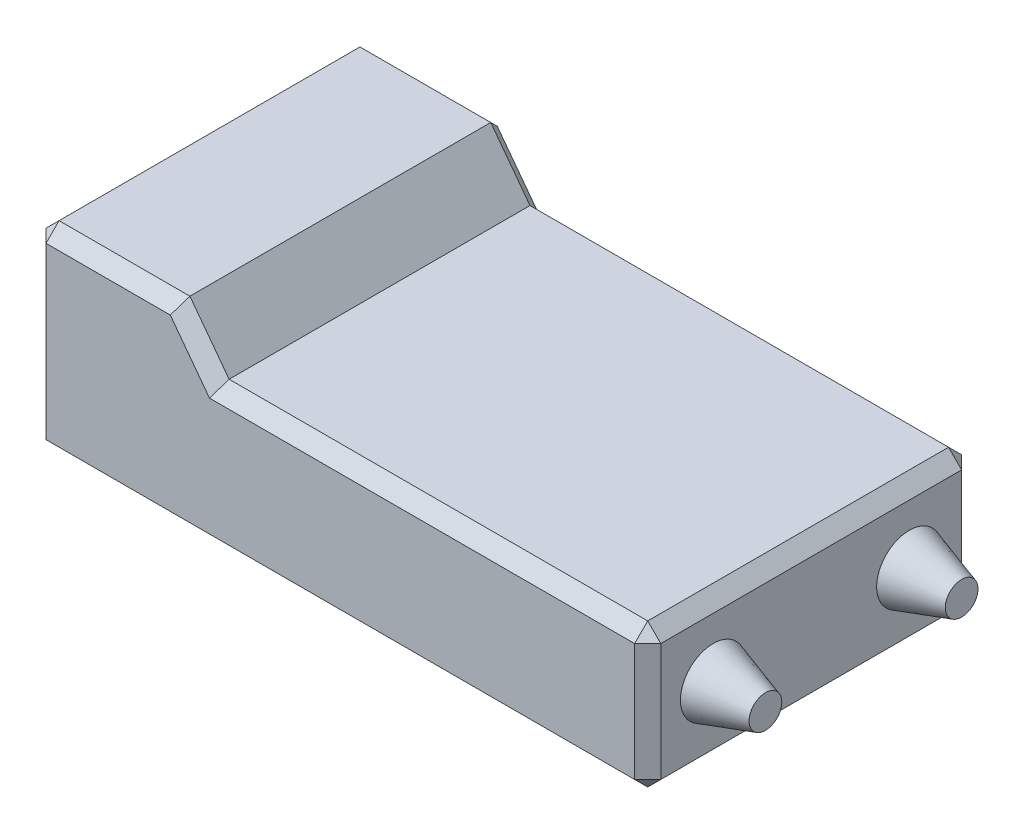
SolidWorks part; units mm, degrees
ref_plane "Front Plane" through (0, 0, 0) normal (0, 0, 1) x (1, 0, 0)
ref_plane "Top Plane" through (0, 0, 0) normal (0, 1, 0) x (1, 0, 0)
ref_plane "Right Plane" through (0, 0, 0) normal (1, 0, 0) x (0, 0, -1)
sketch "Sketch2" plane through (0, 0, 0) normal (0, 1, 0) x (1, 0, 0)
  line L1 (-23.5, 12.5) -> (23.5, 12.5)
  line L2 (-23.5, 12.5) -> (-23.5, -12.5)
  line L3 (-23.5, -12.5) -> (23.5, -12.5)
  line L4 (23.5, 12.5) -> (23.5, -12.5)
  line L5 (-23.5, 12.5) -> (23.5, -12.5) construction
  line L6 (-23.5, -12.5) -> (23.5, 12.5) construction
  point P0 (0, 0)
  dimension "D1" = 25
  dimension "D2" = 47
extrude "Boss-Extrude1" add sketch "Sketch2" along normal blind 11
sketch "Sketch3" plane through (0, 0, 12.5) normal (0, 0, 1) x (1, 0, 0)
  line L0 (-23.5, 11) -> (-9.5, 11)
  line L1 (-23.5, 11) -> (23.5, 11) construction
  line L2 (-9.5, 11) -> (-12.5, 15)
  line L3 (-12.5, 15) -> (-23.5, 15)
  line L4 (-23.5, 15) -> (-23.5, 11)
  dimension "D1" = 11
  dimension "D2" = 14
  dimension "D3" = 4
extrude "Boss-Extrude2" add sketch "Sketch3" against normal up to surface (25 mm away) up to face at (0, 5.5, -12.5)
sketch "Sketch4" plane through (-23.5, 0, 0) normal (-1, 0, 0) x (0, 0, 1)
  line L0 (-12.5, 15) -> (12.5, 15) construction
  line L1 (-10.5, 13) -> (10.5, 13)
  line L2 (-10.5, 13) -> (-10.5, 2)
  line L3 (-10.5, 2) -> (10.5, 2)
  line L4 (10.5, 13) -> (10.5, 2)
  line L5 (-10.5, 13) -> (10.5, 2) construction
  line L6 (-10.5, 2) -> (10.5, 13) construction
  line L7 (12.5, 15) -> (12.5, 0) construction
  line L8 (-12.5, 15) -> (-12.5, 0) construction
  line L9 (-12.5, 0) -> (12.5, 0) construction
  point P0 (0, 7.5)
  dimension "D1" = 2
  dimension "D2" = 2
  dimension "D3" = 2
  dimension "D4" = 2
extrude "Cut-Extrude1" cut sketch "Sketch4" against normal blind 5
sketch "Sketch5" plane through (23.5, 0, 0) normal (1, 0, 0) x (0, 0, -1)
  line L0 (-12.5, 11) -> (-12.5, 0) construction
  line L1 (-12.5, 0) -> (12.5, 0) construction
  circle A0 centre (-7.5, 5.5) radius 2.5
  dimension "D1" = 5
  dimension "D2" = 5
  dimension "D3" = 5.5
ref_plane "Plane1" through (27.5, 0, 0) normal (1, 0, 0) x (0, 0, -1)
sketch "Sketch6" plane through (27.5, 0, 0) normal (1, 0, 0) x (0, 0, -1)
  circle A0 centre (-7.5, 5.5) radius 1.25
  dimension "D1" = 2.5
loft "Loft1" add profiles "Sketch5", "Sketch6"
mirror "Mirror1" about plane through (0, 0, 0) normal (0, 0, 1) of "Loft1"
chamfer "Chamfer1" distance 1 angle 45 16 edges at (23.5, 5.5, -12.5) (7, 11, -12.5) (-11, 13, -12.5) (-11, 13, 12.5) (-18, 15, -12.5) (-18, 15, 12.5) (-23.5, 7.5, -12.5) (0, 0, -12.5) (7, 11, 12.5) (23.5, 0, 0) (-23.5, 0, 0) (-23.5, 15, 0) (-23.5, 7.5, 12.5) (0, 0, 12.5) (23.5, 5.5, 12.5) (23.5, 11, 0)
sketch "Sketch7" plane through (-18.5, 0, 0) normal (-1, 0, 0) x (0, 0, 1)
  line L0 (11.5, 0) -> (-11.5, 0) construction
  line L1 (-8.9276, 4.4543) -> (-8.0724, 4.4543)
  line L2 (-8.9276, 4.4543) -> (-8.9276, 3.5457)
  line L3 (-8.9276, 3.5457) -> (-8.0724, 3.5457)
  line L4 (-8.0724, 4.4543) -> (-8.0724, 3.5457)
  line L5 (-8.9276, 4.4543) -> (-8.0724, 3.5457) construction
  line L6 (-8.9276, 3.5457) -> (-8.0724, 4.4543) construction
  line L7 (-12.5, 1) -> (-12.5, 14) construction
  point P0 (-8.5, 4)
  dimension "D1" = 4
  dimension "D2" = 4
extrude "Boss-Extrude3" add sketch "Sketch7" along normal up to surface (5 mm away) up to face at (-23.5, 7.5, 0)
pattern_linear "LPattern1" count 7 spacing 2.8333 along (0, 0, 1) count 3 spacing 3.5 along (0, 1, 0) of "Boss-Extrude3"
